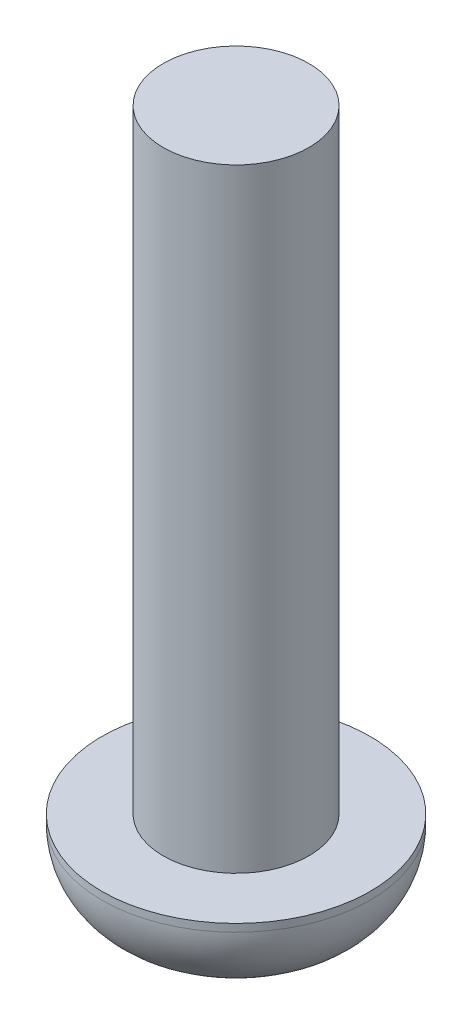
SolidWorks part; units mm, degrees
material "Plain Carbon Steel"
ref_plane "Front Plane" through (0, 0, 0) normal (0, 0, 1) x (1, 0, 0)
ref_plane "Top Plane" through (0, 0, 0) normal (0, 1, 0) x (1, 0, 0)
ref_plane "Right Plane" through (0, 0, 0) normal (1, 0, 0) x (0, 0, -1)
sketch "Sketch1" plane through (0, 0, 0) normal (0, 1, 0) x (1, 0, 0)
  circle A0 centre (0, 0) radius 3.5
  dimension "D1" = 7
extrude "Boss-Extrude1" add sketch "Sketch1" along normal blind 2.2
sketch "Sketch2" plane through (0, 2.2, 0) normal (0, 1, 0) x (1, 0, 0)
  circle A0 centre (0, 0) radius 1.9
  dimension "D1" = 3.8
extrude "Boss-Extrude2" add sketch "Sketch2" along normal blind 16
fillet "Fillet1" radius 2 1 edges at (0, 0, 3.5)
